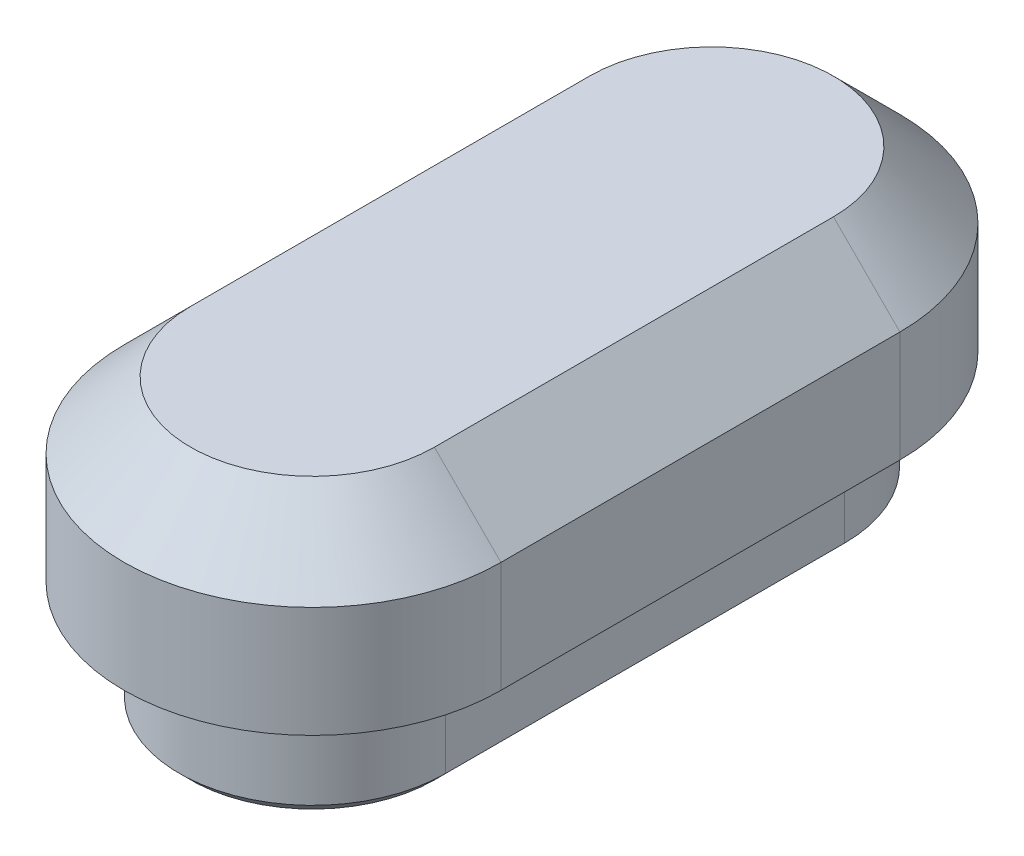
SolidWorks part; units mm, degrees
ref_plane "Plan de face" through (0, 0, 0) normal (0, 0, 1) x (1, 0, 0)
ref_plane "Plan de dessus" through (0, 0, 0) normal (0, 1, 0) x (1, 0, 0)
ref_plane "Plan de droite" through (0, 0, 0) normal (1, 0, 0) x (0, 0, -1)
sketch "Esquisse1" plane through (0, 0, 0) normal (0, 1, 0) x (1, 0, 0)
  line L0 (0, 0) -> (49.3105, 0) construction
  line L1 (0, 0) -> (0, 71.7763) construction
  line L2 (-8.5, 9) -> (-8.5, -9)
  line L4 (8.5, 9) -> (8.5, -9)
  arc A0 (8.5, 9) -> (-8.5, 9) centre (0, 9) ccw
  arc A1 (-8.5, -9) -> (8.5, -9) centre (0, -9) ccw
  dimension "D1" = 35
  dimension "D2" = 17
extrude "Extrusion1" add sketch "Esquisse1" along normal blind 8
chamfer "Chanfrein1" distance 3 angle 45 4 edges at (0, 8, 17.5) (8.5, 8, 0) (0, 8, -17.5) (-8.5, 8, 0)
shell "Coque1" thickness 4
sketch "Esquisse2" plane through (0, 0, 0) normal (0, -1, 0) x (1, 0, 0)
  line L0 (4.5, 9) -> (4.5, -9) construction
  line L1 (-4.5, -9) -> (-4.5, 9) construction
  line L2 (4.5, 9) -> (4.5, -9)
  line L3 (-4.5, -9) -> (-4.5, 9)
  line L4 (-6, -9) -> (-6, 9)
  line L5 (6, 9) -> (6, -9)
  arc A0 (-4.5, -9) -> (4.5, -9) centre (0, -9) ccw construction
  arc A1 (4.5, 9) -> (-4.5, 9) centre (0, 9) ccw construction
  arc A2 (-4.5, -9) -> (4.5, -9) centre (0, -9) ccw
  arc A3 (4.5, 9) -> (-4.5, 9) centre (0, 9) ccw
  arc A4 (6, 9) -> (-6, 9) centre (0, 9) ccw
  arc A5 (-6, -9) -> (6, -9) centre (0, -9) ccw
  dimension "D1" = 1.5
extrude "Extrusion2" add sketch "Esquisse2" along normal blind 5
chamfer "Chanfrein2" distance 0.5 angle 45 4 edges at (0, -5, -15) (6, -5, 0) (0, -5, 15) (-6, -5, 0)
